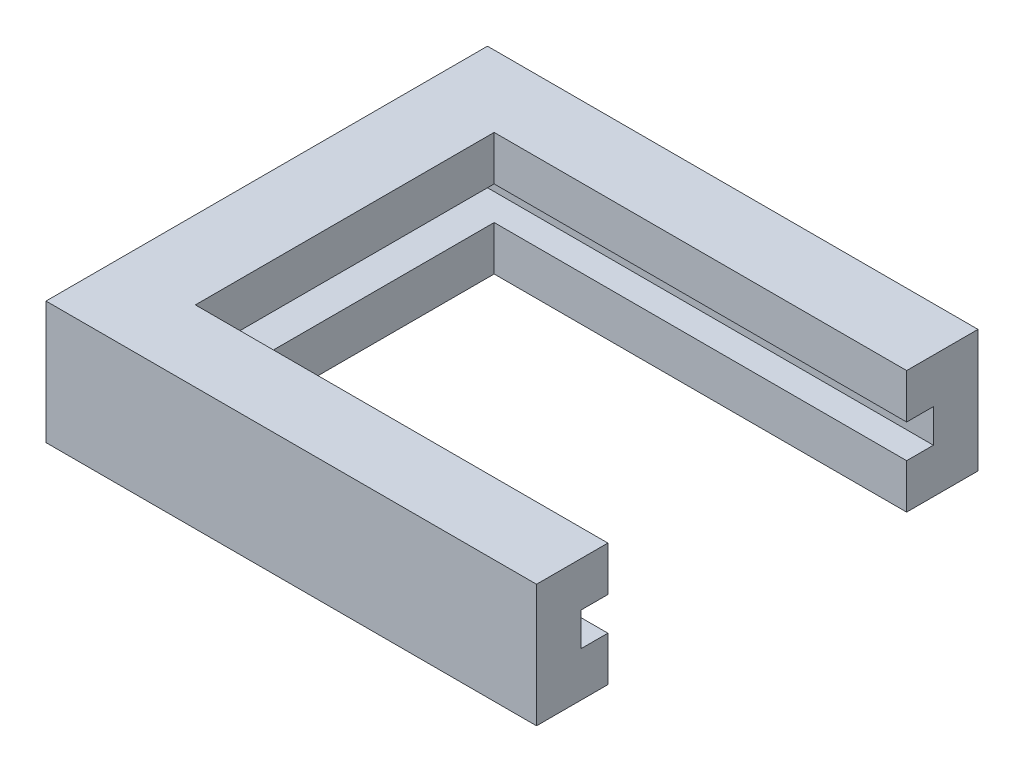
SolidWorks part; units mm, degrees
ref_plane "Front Plane" through (0, 0, 0) normal (0, 0, 1) x (1, 0, 0)
ref_plane "Top Plane" through (0, 0, 0) normal (0, 1, 0) x (1, 0, 0)
ref_plane "Right Plane" through (0, 0, 0) normal (1, 0, 0) x (0, 0, -1)
sketch "Sketch1" plane through (0, 0, 0) normal (1, 0, 0) x (0, 0, -1)
  line L0 (-12.6882, 0.973) -> (3.1118, 0.973)
  line L1 (-12.5882, -0.427) -> (3.0118, -0.427) construction
  line L2 (-12.5882, -0.427) -> (-12.5882, 0.873) construction
  line L3 (-12.5882, 0.873) -> (3.0118, 0.873) construction
  line L4 (3.0118, -0.427) -> (3.0118, 0.873) construction
  line L5 (3.1118, 0.973) -> (3.1118, -0.527)
  line L6 (3.1118, -0.527) -> (-12.6882, -0.527)
  line L7 (-12.6882, -0.527) -> (-12.6882, 0.973)
  line L9 (-14.6882, 2.973) -> (5.1118, 2.973)
  line L10 (-14.6882, 2.973) -> (-14.6882, -2.527)
  line L11 (-14.6882, -2.527) -> (5.1118, -2.527)
  line L12 (5.1118, 2.973) -> (5.1118, -2.527)
  point P8 (-12.6882, 0.223)
  point P9 (-12.5882, 0.223)
  point P10 (-4.7882, 0.973)
  point P11 (-4.7882, 0.873)
  dimension "D1" = 1.3
  dimension "D2" = 15.6
  dimension "D3" = 15.8
  dimension "D4" = 1.5
  dimension "D5" = 2
  dimension "D6" = 2
  dimension "D7" = 2
  dimension "D8" = 2
extrude "Boss-Extrude1" add sketch "Sketch1" along normal blind 20.5
sketch "Sketch2" plane through (0, 2.973, 0) normal (0, 1, 0) x (1, 0, 0)
  line L0 (20.5, 5.1118) -> (20.5, -14.6882) construction
  line L1 (20.5, -11.4882) -> (2, -11.4882)
  line L2 (20.5, -11.4882) -> (20.5, 1.9118)
  line L3 (20.5, 1.9118) -> (2, 1.9118)
  line L4 (2, -11.4882) -> (2, 1.9118)
  line L6 (20.5, 5.1118) -> (0, 5.1118) construction
  line L7 (20.5, -14.6882) -> (0, -14.6882) construction
  line L8 (0, 5.1118) -> (0, -14.6882) construction
  dimension "D1" = 3.2
  dimension "D2" = 3.2
  dimension "D3" = 2
extrude "Cut-Extrude1" cut sketch "Sketch2" against normal through all
sketch "Sketch3" plane through (0, 0, 0) normal (-1, 0, 0) x (0, 0, 1)
  line L1 (-5.1118, 2.973) -> (14.6882, 2.973)
  line L2 (-5.1118, 2.973) -> (-5.1118, -2.527)
  line L3 (-5.1118, -2.527) -> (14.6882, -2.527)
  line L4 (14.6882, 2.973) -> (14.6882, -2.527)
extrude "Boss-Extrude2" add sketch "Sketch3" along normal blind 1.5
